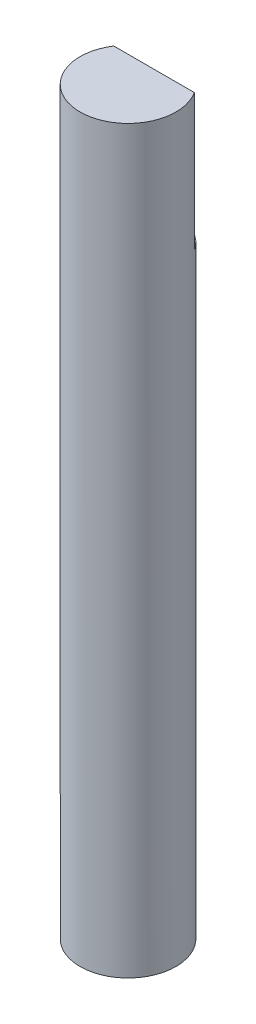
SolidWorks part; units mm, degrees
ref_plane "前视基准面" through (0, 0, 0) normal (0, 0, 1) x (1, 0, 0)
ref_plane "上视基准面" through (0, 0, 0) normal (0, 1, 0) x (1, 0, 0)
ref_plane "右视基准面" through (0, 0, 0) normal (1, 0, 0) x (0, 0, -1)
sketch "草图1" plane through (0, 0, 0) normal (0, 1, 0) x (1, 0, 0)
  circle A0 centre (0, 0) radius 3.5
  dimension "D1" = 7
extrude "凸台-拉伸1" add sketch "草图1" along normal blind 54
sketch "草图2" plane through (0, 54, 0) normal (0, 1, 0) x (1, 0, 0)
  line L1 (-4.3948, 11.9) -> (4.3948, 11.9)
  line L2 (-4.3948, 11.9) -> (-4.3948, 1.9)
  line L3 (-4.3948, 1.9) -> (4.3948, 1.9)
  line L4 (4.3948, 11.9) -> (4.3948, 1.9)
  line L5 (-4.3948, 11.9) -> (4.3948, 1.9) construction
  line L6 (-4.3948, 1.9) -> (4.3948, 11.9) construction
  circle A0 centre (0, 0) radius 3.5 construction
  point P0 (0, 6.9)
  dimension "D1" = 1.9
  dimension "D2" = 10
extrude "切除-拉伸1" cut sketch "草图2" against normal blind 10
